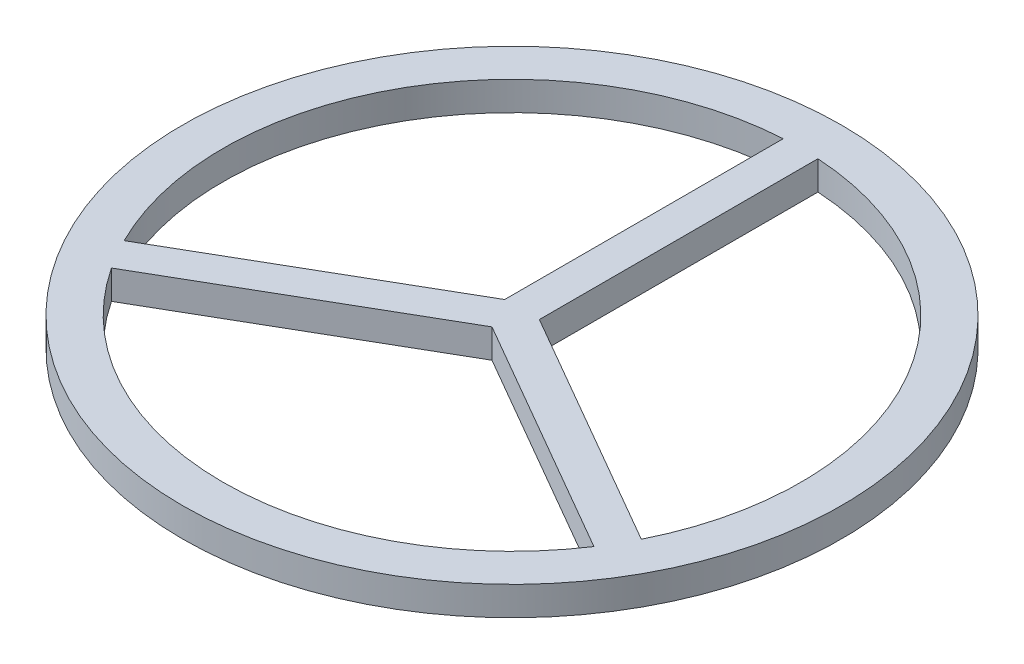
SolidWorks part; units mm, degrees
material "ABS"
ref_plane "Front Plane" through (0, 0, 0) normal (0, 0, 1) x (1, 0, 0)
ref_plane "Top Plane" through (0, 0, 0) normal (0, 1, 0) x (1, 0, 0)
ref_plane "Right Plane" through (0, 0, 0) normal (1, 0, 0) x (0, 0, -1)
sketch "Sketch1" plane through (0, 0, 0) normal (0, 1, 0) x (1, 0, 0)
  circle A0 centre (0, 0) radius 25
  circle A1 centre (0, 0) radius 28.5
  dimension "D1" = 50
  dimension "D2" = 3.5
extrude "Boss-Extrude1" add sketch "Sketch1" along normal blind 2.5
sketch "Sketch2" plane through (0, 2.5, 0) normal (0, 1, 0) x (1, 0, 0)
  line L0 (0, 0) -> (0, 25) construction
  line L5 (0, 0) -> (-21.6506, -12.5) construction
  line L6 (0, 0) -> (21.6506, -12.5) construction
  line L7 (-1.5, 0.866) -> (-22.4006, -11.201)
  line L8 (1.5, 0.866) -> (1.5, 25)
  line L9 (0, -1.7321) -> (20.9006, -13.799)
  line L10 (0, -1.7321) -> (-20.9006, -13.799)
  line L11 (-1.5, 0.866) -> (-1.5, 25)
  line L12 (1.5, 0.866) -> (22.4006, -11.201)
  line L13 (-0.75, 1.299) -> (-22.4006, -11.201) construction
  line L14 (-1.5, 0) -> (-1.5, 25) construction
  line L15 (0.75, 1.299) -> (22.4006, -11.201) construction
  line L16 (1.5, 0) -> (1.5, 25) construction
  line L17 (0.75, -1.299) -> (-20.9006, -13.799) construction
  line L18 (-0.75, -1.299) -> (20.9006, -13.799) construction
  line L19 (22.4006, -11.201) -> (20.9006, -13.799)
  line L20 (-20.9006, -13.799) -> (-22.4006, -11.201)
  line L21 (1.5, 25) -> (-1.5, 25)
  circle A0 centre (0, 0) radius 25 construction
  dimension "D1" = 120
  dimension "D2" = 120
  dimension "D3" = 1.5
  dimension "D4" = 1.5
extrude "Boss-Extrude2" add sketch "Sketch2" against normal up to surface (2.5 mm away) up to face at (0, 0, 28.5)
